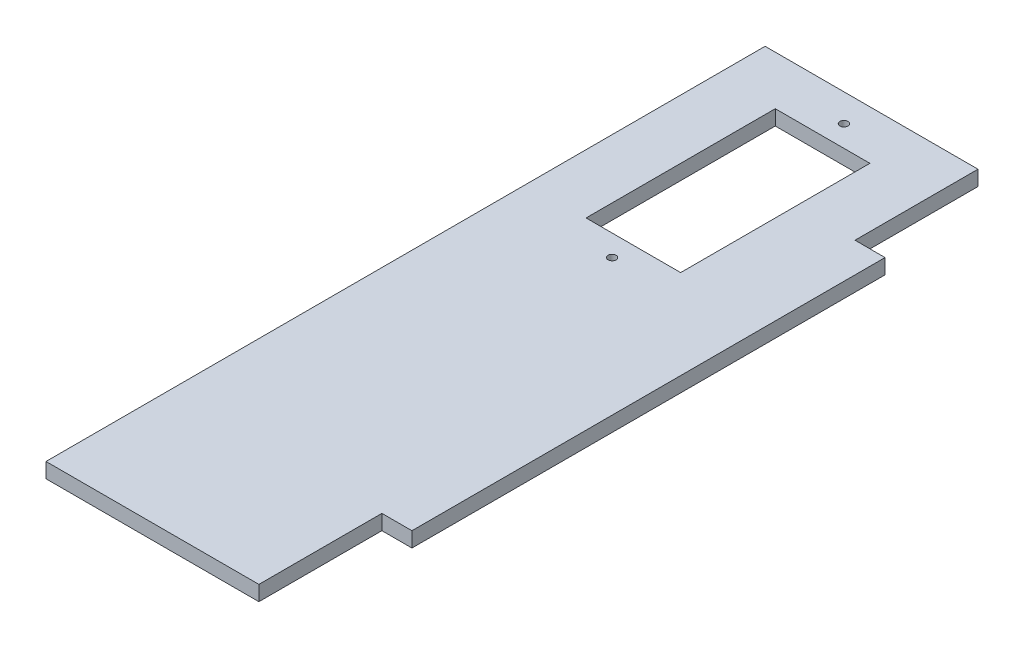
SolidWorks part; units mm, degrees
material "Cedar"
ref_plane "Front Plane" through (0, 0, 0) normal (0, 0, 1) x (1, 0, 0)
ref_plane "Top Plane" through (0, 0, 0) normal (0, 1, 0) x (1, 0, 0)
ref_plane "Right Plane" through (0, 0, 0) normal (1, 0, 0) x (0, 0, -1)
sketch "Sketch1" plane through (0, 0, 0) normal (0, 1, 0) x (1, 0, 0)
  line L0 (-22.5, 26) -> (22.5, 26)
  line L1 (22.5, 26) -> (22.5, 0)
  line L2 (22.5, 0) -> (28.85, 0)
  line L3 (28.85, 0) -> (28.85, -100)
  line L4 (28.85, -100) -> (22.5, -100)
  line L5 (22.5, -100) -> (22.5, -126)
  line L6 (22.5, -126) -> (-22.5, -126)
  line L7 (-22.5, -126) -> (-22.5, -100)
  line L8 (-22.5, -100) -> (-28.85, -100)
  line L9 (-28.85, -100) -> (-28.85, 0)
  line L10 (-28.85, 0) -> (-22.5, 0)
  line L11 (-22.5, 0) -> (-22.5, 26)
  line L12 (-22.5, 0) -> (-22.5, -100) construction
  point P11 (0, 26)
  point P14 (-28.85, -50)
  dimension "D1" = 6.35
  dimension "D2" = 100
  dimension "D3" = 45
  dimension "D4" = 152
extrude "Boss-Extrude1" add sketch "Sketch1" along normal blind 3.175 contours L11 L12 L7 L6 L5 L4 L3 L2 L1 L0
sketch "Sketch2" plane through (0, 3.175, 0) normal (0, 1, 0) x (1, 0, 0)
  line L0 (22.5, -126) -> (-22.5, -126) construction
  line L1 (10, 15.65) -> (-10, 15.65)
  line L2 (10, 15.65) -> (10, -24.35)
  line L3 (10, -24.35) -> (-10, -24.35)
  line L4 (-10, 15.65) -> (-10, -24.35)
  line L5 (0, 20.15) -> (0, -28.85) construction
  point P4 (0, -18)
  point P5 (0, -24.35)
  point P9 (0, 20.15)
  point P10 (0, -28.85)
  point P13 (10, -4.35)
  point P14 (0, -4.35)
  dimension "D1" = 108
  dimension "D2" = 20
  dimension "D3" = 40
  dimension "D4" = 6.35
  dimension "D5" = 49
extrude "Cut-Extrude1" cut sketch "Sketch2" against normal through all
hole_wizard "M1.6 Clearance Hole1" positions "Sketch6" profile "Sketch5" hole size "M1.6" standard "ANSI Metric" end condition through all
sketch "Sketch6" plane through (0, 3.175, 0) normal (0, 1, 0) x (1, 0, 0)
  point P0 (0, -28.85)
  point P3 (0, 20.15)
sketch "Sketch5" plane through (0, 3.175, 28.85) normal (1, 0, 0) x (0, 0, 1)
  line L0 (0, 0) -> (0, 3.175)
  line L1 (0, 3.175) -> (0.85, 3.175)
  line L2 (0.85, 3.175) -> (0.85, 0)
  line L5 (0.85, 0) -> (0, 0)
  line L11 (0, -6.35) -> (0, 107.95) construction
  dimension "Thru Hole Dia." = 1.7
  dimension "Thru Hole Depth" = 3.175
equation "\"length\"= 152mm"
equation "\"w_mach\"= 45mm"
equation "\"w_tab\"= 100mm"
equation "\"t_wood\"= 0.125in"
equation "\"t_side\"= 0.25in"
equation "\"D1@Sketch1\"=\"t_side\""
equation "\"D2@Sketch1\"=\"w_tab\""
equation "\"D3@Sketch1\"=\"w_mach\""
equation "\"D4@Sketch1\"=\"length\""
equation "\"D1@Boss-Extrude1\"=\"t_wood\""
equation "\"dX\"= 123mm"
equation "\"in_rad\"= 15mm"
equation "\"D1@Sketch2\"=\"dX\"-\"in_rad\""
equation "\"w_servo\"= 20mm"
equation "\"l_servo\"= 40mm"
equation "\"servocenter\"= 6.35mm"
equation "\"D2@Sketch2\"=\"w_servo\""
equation "\"D3@Sketch2\"=\"l_servo\""
equation "\"D4@Sketch2\"=\"servocenter\""
equation "\"servoholes\"= 49mm"
equation "\"D5@Sketch2\"=\"servoholes\""
